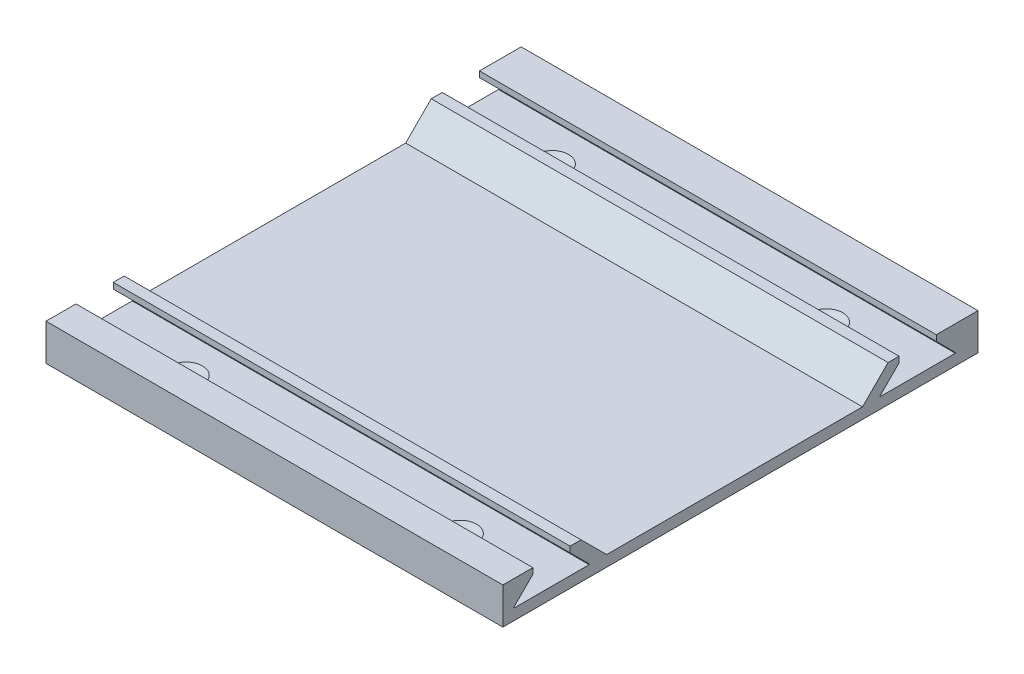
SolidWorks part; units mm, degrees
ref_plane "Plan de face" through (0, 0, 0) normal (0, 0, 1) x (1, 0, 0)
ref_plane "Plan de dessus" through (0, 0, 0) normal (0, 1, 0) x (1, 0, 0)
ref_plane "Plan de droite" through (0, 0, 0) normal (1, 0, 0) x (0, 0, -1)
sketch "Esquisse1" plane through (0, 0, 0) normal (0, 1, 0) x (1, 0, 0)
  line L1 (0, 0) -> (125, 0)
  line L2 (0, 0) -> (0, 130)
  line L3 (0, 130) -> (125, 130)
  line L4 (125, 0) -> (125, 130)
  dimension "D1" = 125
  dimension "D2" = 130
extrude "Boss.-Extru.1" add sketch "Esquisse1" along normal blind 10
sketch "Esquisse2" plane through (125, 0, 0) normal (1, 0, 0) x (0, 0, -1)
  line L0 (8.2, 10) -> (8.2, 8.4)
  line L1 (0, 10) -> (130, 10) construction
  line L2 (8.2, 8.4) -> (3, 3.2)
  line L3 (0, 10) -> (0, 0) construction
  line L4 (0, 0) -> (130, 0) construction
  line L5 (13.3, 10) -> (13.3, 0) construction
  line L7 (18.4, 8.4) -> (23.6, 3.2)
  line L8 (18.4, 10) -> (18.4, 8.4)
  line L9 (3, 3) -> (23.6, 3)
  line L10 (23.6, 3) -> (23.6, 3.2)
  line L11 (63.4, 10) -> (63.4, 0) construction
  line L12 (3, 3) -> (3, 3.2)
  line L13 (8.2, 10) -> (18.4, 10)
  line L22 (118.6, 10) -> (118.6, 8.4)
  line L23 (118.6, 8.4) -> (123.8, 3.2)
  line L24 (123.8, 3) -> (123.8, 3.2)
  line L25 (123.8, 3) -> (103.2, 3)
  line L26 (103.2, 3) -> (103.2, 3.2)
  line L27 (108.4, 8.4) -> (103.2, 3.2)
  line L28 (108.4, 10) -> (108.4, 8.4)
  line L29 (118.6, 10) -> (108.4, 10)
  dimension "D1" = 45
  dimension "D2" = 5.2
  dimension "D3" = 3
  dimension "D4" = 5.1
  dimension "D5" = 3
  dimension "D6" = 0.2
  dimension "D7" = 0.2
  dimension "D8" = 45
extrude "Enlèv. mat.-Extru.1" cut sketch "Esquisse2" against normal up to surface (125 mm away) up to face at (0, 5, -65)
ref_plane "Plan1" through (0, 0, -63.4) normal (0, 0, -1) x (-1, 0, 0)
ref_plane "Plan2" through (0, 6.5, 0) normal (0, 1, 0) x (1, 0, 0)
ref_plane "Plan3" through (62.5, 0, 0) normal (1, 0, 0) x (0, 0, -1)
sketch "Esquisse4" plane through (0, 3, 0) normal (0, 1, 0) x (1, 0, 0)
  line L0 (125, 3) -> (125, 23.6) construction
  line L1 (125, 13.3) -> (0, 13.3) construction
  line L2 (0, 23.6) -> (0, 3) construction
  line L3 (62.5, -5.5) -> (62.5, 5.5) construction
  line L4 (0.88, 63.4) -> (-0.88, 63.4) construction
  circle A1 centre (100, 13.3) radius 2.5
  circle A2 centre (25, 13.3) radius 2.5
  circle A3 centre (100, 113.5) radius 2.5
  circle A4 centre (25, 113.5) radius 2.5
  point P4 (0, 0)
  dimension "D1" = 5
  dimension "D2" = 25
extrude "Enlèv. mat.-Extru.2" cut sketch "Esquisse4" against normal up to surface (3 mm away) up to face at (62.5, 0, -65)
chamfer "Chanfrein2" distance 2 angle 45 4 edges at (25, 3, -111) (100, 3, -116) (100, 3, -10.8) (25, 3, -15.8)
sketch "Esquisse8" plane through (0, 0, 0) normal (-1, 0, 0) x (0, 0, 1)
  line L0 (-104.0895, 8.6895) -> (-98.4791, 3.0791)
  line L1 (-98.4791, 3.0791) -> (-95.4, 0)
  line L2 (-130, 0) -> (0, 0) construction
  line L3 (-104.0895, 8.6895) -> (-105.4, 10)
  line L4 (-108.4, 10) -> (-18.4, 10) construction
  line L5 (-108.4, 8.4) -> (-108.4, 10) construction
  line L6 (-103.2, 3.2) -> (-108.4, 8.4) construction
  line L7 (-63.4, 0.88) -> (-63.4, -0.88) construction
  line L8 (-22.7105, 8.6895) -> (-21.4, 10)
  line L9 (-22.7105, 8.6895) -> (-28.3209, 3.0791)
  line L10 (-28.3209, 3.0791) -> (-31.4, 0)
  line L11 (-95.4, 0) -> (-31.4, 0)
  line L12 (-21.4, 10) -> (-105.4, 10)
  line L13 (-98.4, 3) -> (-28.4, 3)
  line M11 (-18.4, 10) -> (-108.4, 10)
  dimension "D1" = 180
  dimension "D2" = 3
  dimension "D3" = 0
  dimension "D4" = 3
extrude "Enlèv. mat.-Extru.6" cut sketch "Esquisse8" against normal through all contours L1 L13 L10 L9 L8 L3 L0 M11
